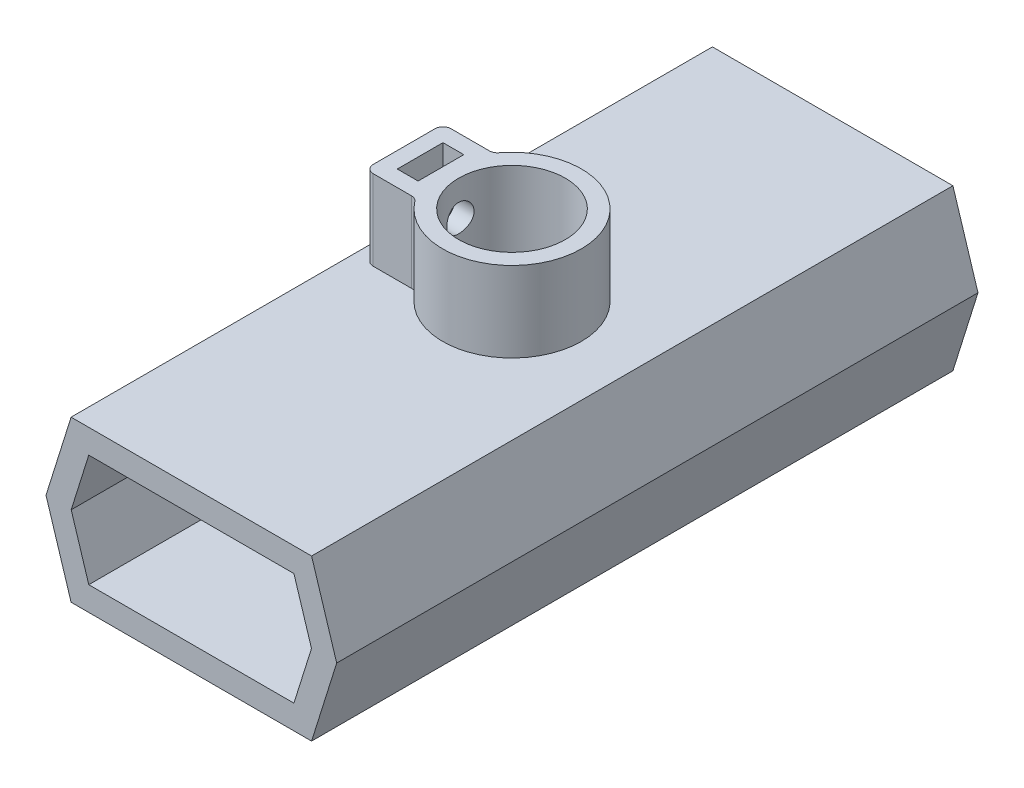
SolidWorks part; units mm, degrees
ref_plane "前视基准面" through (0, 0, 0) normal (0, 0, 1) x (1, 0, 0)
ref_plane "上视基准面" through (0, 0, 0) normal (0, 1, 0) x (1, 0, 0)
ref_plane "右视基准面" through (0, 0, 0) normal (1, 0, 0) x (0, 0, -1)
sketch "草图1" plane through (0, 0, 0) normal (0, 0, 1) x (1, 0, 0)
  line L0 (-15, 0) -> (15, 0)
  line L1 (15, 0) -> (18.1304, -10)
  line L2 (18.1304, -10) -> (15, -20)
  line L3 (15, -20) -> (-15, -20)
  line L4 (-15, -20) -> (-18.1304, -10)
  line L5 (-18.1304, -10) -> (-15, 0)
  point P6 (0, 0)
  point P9 (0, -20)
  dimension "D1" = 30
  dimension "D2" = 20
extrude "凸台-拉伸1" add sketch "草图1" along normal mid plane 80
sketch "草图7" plane through (0, 0, -40) normal (0, 0, -1) x (-1, 0, 0)
  line L12 (14.9869, -10) -> (12.7956, -3)
  line L13 (12.7956, -3) -> (-12.7956, -3)
  line L14 (-12.7956, -3) -> (-14.9869, -10)
  line L15 (-14.9869, -10) -> (-12.7956, -17)
  line L16 (-12.7956, -17) -> (12.7956, -17)
  line L17 (12.7956, -17) -> (14.9869, -10)
  line L18 (14.9869, -10) -> (12.7956, -3)
  line L19 (12.7956, -3) -> (-12.7956, -3)
  line L20 (-12.7956, -3) -> (-14.9869, -10)
  line L21 (-14.9869, -10) -> (-12.7956, -17)
  line L22 (-12.7956, -17) -> (12.7956, -17)
  line L23 (12.7956, -17) -> (14.9869, -10)
  dimension "D1" = 3
extrude "切除-拉伸3" cut sketch "草图7" against normal through all
sketch "草图8" plane through (0, 0, 0) normal (0, 1, 0) x (1, 0, 0)
  circle A0 centre (0, 0) radius 6.65
  dimension "D1" = 13.3
extrude "切除-拉伸4" cut sketch "草图8" against normal through all
sketch "草图9" plane through (0, 0, 0) normal (0, 1, 0) x (1, 0, 0)
  circle A0 centre (0, 0) radius 6.65
  circle A1 centre (0, 0) radius 8.65
  circle A2 centre (0, 0) radius 6.65 construction
  dimension "D1" = 2
extrude "凸台-拉伸2" add sketch "草图9" along normal blind 10
sketch "草图10" plane through (0, 0, 0) normal (0, 1, 0) x (1, 0, 0)
  line L0 (-7.1587, 4.8555) -> (-13.4616, 4.8555)
  line L1 (-13.4616, 4.8555) -> (-13.4616, -4.8555)
  line L2 (-13.4616, -4.8555) -> (-7.1587, -4.8555)
  line L4 (-11.4616, 2.85) -> (-8.8616, 2.85)
  line L5 (-11.4616, 2.85) -> (-11.4616, -2.85)
  line L6 (-11.4616, -2.85) -> (-8.8616, -2.85)
  line L7 (-8.8616, 2.85) -> (-8.8616, -2.85)
  circle A0 centre (0, 0) radius 8.65 construction
  arc A1 (-7.1587, 4.8555) -> (-7.1587, -4.8555) centre (0, 0) ccw
  point P10 (-13.4616, 0)
  point P11 (-11.4616, 0)
  point P12 (-13.1883, 4.3615)
  point P13 (-13.4616, 4.8555)
  point P14 (-8.8616, 0)
  circle M10 centre (0, 0) radius 8.65
  dimension "D1" = 2.6
  dimension "D2" = 5.7
  dimension "D3" = 2
extrude "凸台-拉伸3" add sketch "草图10" along normal blind 10 contours L4 L7 L0 L1 L2 L6 L5 M10
sketch "草图11" plane through (-13.4616, 0, 0) normal (-1, 0, 0) x (0, 0, 1)
  circle A0 centre (0, 5.6847) radius 1.7
  point P2 (0, 0)
  point P4 (0, 0)
  dimension "D1" = 3.4
extrude "切除-拉伸5" cut sketch "草图11" against normal blind 10
fillet "圆角1" radius 1 4 edges at (-7.1587, 5, -4.8555) (-13.4616, 5, -4.8555) (-13.4616, 5, 4.8555) (-7.1587, 5, 4.8555)
